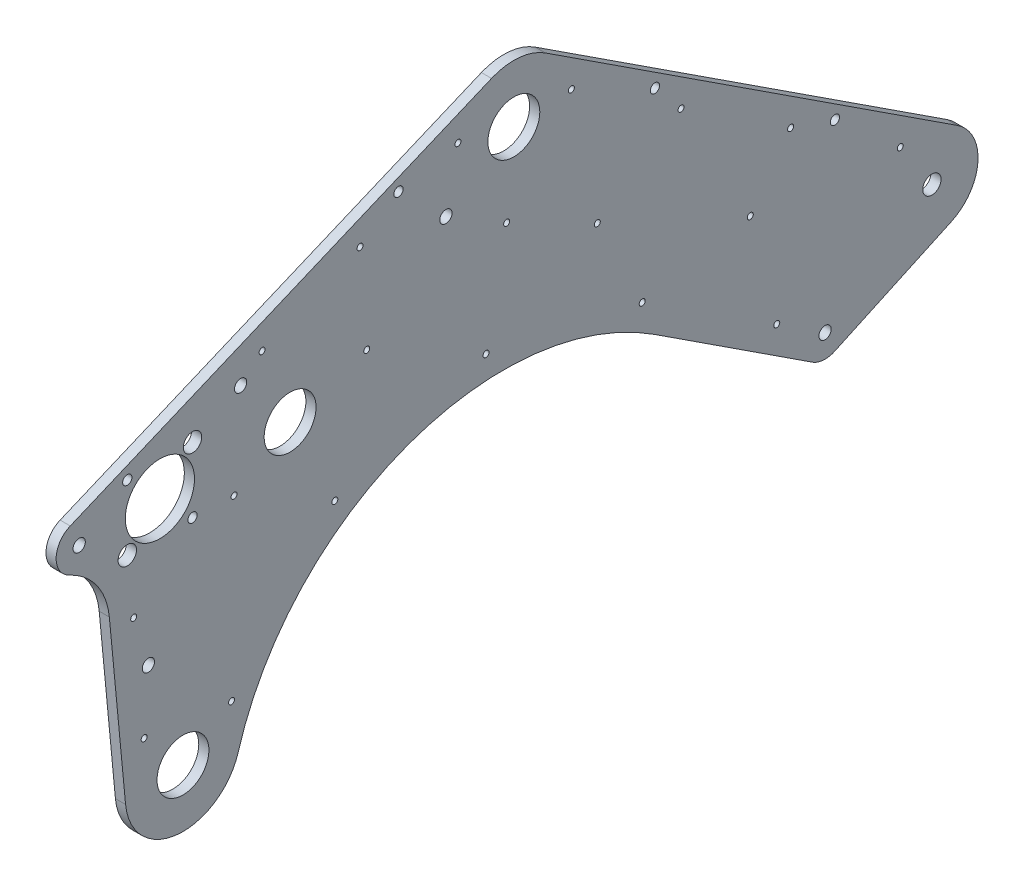
SolidWorks part; units mm, degrees
material "Acrylic (Medium-high impact)"
ref_plane "Front" through (0, 0, 0) normal (0, 0, 1) x (1, 0, 0)
ref_plane "Top" through (0, 0, 0) normal (0, 1, 0) x (1, 0, 0)
ref_plane "Right" through (0, 0, 0) normal (1, 0, 0) x (0, 0, -1)
sketch "Sketch1" plane through (0, 0, 0) normal (1, 0, 0) x (0, 0, -1)
  line L0 (-109.5375, -69.85) -> (-109.5375, -196.85)
  line L1 (-109.5375, -196.85) -> (-160.3375, -196.85)
  line L2 (-192.0875, -165.1) -> (-192.0875, -101.6)
  line L3 (-160.3375, -69.85) -> (-109.5375, -69.85)
  line L4 (-28.6872, -260.35) -> (-968.3377, -260.35) construction
  line L5 (-414.3375, -165.1) -> (-414.3375, -101.6) construction
  line L6 (-101.6, -57.15) -> (-76.2, -57.15)
  line L7 (-101.6, -57.15) -> (-101.6, -82.55)
  line L8 (-101.6, -82.55) -> (-76.2, -82.55)
  line L9 (-76.2, -57.15) -> (-76.2, -82.55)
  line L10 (-160.3375, 152.4) -> (-109.5375, 152.4) construction
  line L11 (-412.4442, -70.6452) -> (-160.3375, -101.6) construction
  line L12 (-353.4405, 63.4068) -> (-160.3375, -101.6) construction
  line L13 (-230.2306, 142.5945) -> (-160.3375, -101.6) construction
  line L14 (-435.3258, -60.5737) -> (-376.322, 73.4782)
  line L15 (-330.5589, 53.3353) -> (-389.5627, -80.7166)
  line L16 (-366.9572, 84.4377) -> (-243.7472, 163.6254)
  line L17 (-109.5375, -69.85) -> (-109.5375, 357.098) construction
  line L18 (-216.7139, 121.5636) -> (-339.9238, 42.3759)
  line L19 (-515.9375, 289.2974) -> (-515.9375, -104.2984) construction
  line L22 (-400.2568, 65.0845) -> (-387.5568, -68.2751)
  line L23 (-437.3316, -73.0152) -> (-450.0316, 60.3444)
  circle A0 centre (0, 0) radius 5.0419
  circle A1 centre (-412.4442, -70.6452) radius 11.557
  circle A2 centre (-353.4405, 63.4068) radius 11.557
  circle A3 centre (-230.2306, 142.5945) radius 11.557
  arc A4 (-160.3375, -196.85) -> (-192.0875, -165.1) centre (-160.3375, -165.1) cw
  arc A5 (-192.0875, -101.6) -> (-160.3375, -69.85) centre (-160.3375, -101.6) cw
  circle A6 centre (-309.0551, -144.1658) radius 120.65
  arc A7 (-414.3375, -101.6) -> (-160.3375, 152.4) centre (-160.3375, -101.6) cw construction
  circle A12 centre (-425.1442, 62.7144) radius 31.75
  arc A15 (-389.5627, -80.7166) -> (-435.3258, -60.5737) centre (-412.4442, -70.6452) cw
  arc A16 (-376.322, 73.4782) -> (-330.5589, 53.3353) centre (-353.4405, 63.4068) cw
  arc A17 (-339.9238, 42.3759) -> (-366.9572, 84.4377) centre (-353.4405, 63.4068) cw
  arc A18 (-243.7472, 163.6254) -> (-216.7139, 121.5636) centre (-230.2306, 142.5945) cw
  arc A21 (-450.0316, 60.3444) -> (-400.2568, 65.0845) centre (-425.1442, 62.7144) cw
  arc A22 (-387.5568, -68.2751) -> (-437.3316, -73.0152) centre (-412.4442, -70.6452) cw
  circle B0 centre (-230.2306, 142.5945) radius 25
  circle B1 centre (-353.4405, 63.4068) radius 25
  circle B2 centre (-412.4442, -70.6452) radius 25
  circle B3 centre (-425.1442, 62.7144) radius 25
  dimension "D1" = 10.0838
  dimension "D2" = 23.114
  dimension "D4" = 31.75
  dimension "D10" = 241.3
  dimension "D19" = 63.5
  dimension "D26" = 70.6452
  dimension "D27" = 412.4442
  dimension "D3" = 127
  dimension "D5" = 82.55
  dimension "D6" = 190.5
  dimension "D7" = 25.4
  dimension "D8" = 7.9375
  dimension "D9" = 203.2
  dimension "D12" = 101.6
  dimension "D13" = 57.15
  dimension "D14" = 33.514
  dimension "D15" = 33.514
  dimension "D16" = 7
  dimension "D24" = 406.4
  dimension "D21" = 12.7
  dimension "D11" = 222.25
sketch_block_instance "Block1-1"
sketch_block "Block1" parameters "D1"=50
sketch_block_instance "Block2-1"
sketch_block "Block2" parameters "D1"=40
sketch_block_instance "Block3-1"
sketch_block "Block3" parameters "D1"=40
sketch_block_instance "Block4-1"
sketch_block "Block4" parameters "D1"=50
other "Belt1"
other "Belt2"
other "Belt4"
sketch "Sketch3" plane through (0, 0, 0) normal (1, 0, 0) x (0, 0, -1)
  line L0 (-412.4442, -70.6452) -> (0, 0) construction
  line L1 (0, 0) -> (-58.8496, -41.2069) construction
  line L2 (0, 0) -> (-70.6452, 412.4442) construction
  line L3 (0, 0) -> (-41.2069, 58.8496) construction
  line L4 (-58.8496, -41.2069) -> (-64.0291, -10.9672) construction
  line L5 (-41.2069, 58.8496) -> (-10.9672, 64.0291) construction
  line L6 (-41.2069, 58.8496) -> (-58.8496, -41.2069)
  line L7 (-0.9596, 287.1034) -> (-41.2069, 58.8496)
  line L8 (0, 0) -> (142.5945, 230.2306) construction
  line L9 (0, 0) -> (-230.2306, 142.5945) construction
  line L10 (-230.2306, 142.5945) -> (-199.9405, -34.2466) construction
  line L11 (142.5945, 230.2306) -> (-34.2466, 199.9405) construction
  circle A0 centre (-70.6452, 412.4442) radius 25.4
  dimension "D1" = 50.8
  dimension "D2" = 90
  dimension "D3" = 101.6
  dimension "D4" = 231.775
  dimension "D5" = 80
sketch "Sketch2" plane through (0, 0, 0) normal (1, 0, 0) x (0, 0, -1)
  line L0 (-444.0512, -73.6552) -> (-452.991, 20.2192)
  line L1 (-474.5125, 74.4234) -> (-242.5262, 171.867)
  line L2 (-412.4442, -70.6452) -> (-412.4442, 0) construction
  line L4 (13.8769, 21.2742) -> (-212.8845, 169.1873)
  line L7 (-65.788, -51.844) -> (-152.593, 4.7776)
  line L10 (-53.5189, -52.734) -> (10.6613, -23.0542)
  line L13 (-443.1047, 44.7539) -> (-407.1837, 80.675) construction
  line L14 (-443.1047, 80.675) -> (-407.1837, 44.7539) construction
  line L15 (-353.4405, 63.4068) -> (-230.2306, 142.5945) construction
  circle A0 centre (-230.2306, 142.5945) radius 14.2875
  circle A1 centre (-353.4405, 63.4068) radius 14.2875
  circle A2 centre (-412.4442, -70.6452) radius 14.2875
  circle A3 centre (-425.1442, 62.7144) radius 19.05
  circle A9 centre (0, 0) radius 5.0419 construction
  circle A10 centre (0, 0) radius 5.0419
  arc A13 (-444.0512, -73.6552) -> (-381.9977, -79.6491) centre (-412.4442, -70.6452) ccw
  arc A16 (10.6613, -23.0542) -> (13.8769, 21.2742) centre (0, 0) ccw
  arc A18 (-152.593, 4.7776) -> (-381.9977, -79.6491) centre (-235.8542, -122.8677) ccw
  circle A19 centre (-58.8496, -41.2069) radius 3.3782
  circle A22 centre (-267.6235, 118.5618) radius 3.3782
  circle A24 centre (-230.2306, 142.5945) radius 31.75 construction
  circle A27 centre (-407.1837, 80.675) radius 5.08
  circle A28 centre (-443.1047, 80.675) radius 2.5527
  circle A29 centre (-443.1047, 44.7539) radius 5.08
  circle A30 centre (-407.1837, 44.7539) radius 2.5527
  circle A31 centre (-425.1442, 62.7144) radius 25.4 construction
  circle A32 centre (-469.5942, 62.7144) radius 3.3782
  arc A34 (-474.5125, 74.4234) -> (-474.9255, 51.1876) centre (-469.5942, 62.7144) ccw
  arc A35 (-474.9255, 51.1876) -> (-452.991, 20.2192) centre (-490.9194, 16.6072) cw
  circle A37 centre (-425.1442, 62.7144) radius 31.75 construction
  circle A38 centre (-469.5942, 62.7144) radius 7.9375 construction
  circle A39 centre (-431.4942, -13.4856) radius 3.3782
  circle A40 centre (-431.4942, -13.4856) radius 7.9375 construction
  circle A41 centre (-380.6942, 94.4644) radius 3.3782
  arc A42 (-65.788, -51.844) -> (-53.5189, -52.734) centre (-58.8496, -41.2069) ccw
  arc A43 (-242.5262, 171.867) -> (-212.8845, 169.1873) centre (-230.2306, 142.5945) cw
  circle A44 centre (-353.4405, 63.4068) radius 11.557 construction
  point P5 (0, 0)
  dimension "D1" = 28.575
  dimension "D2" = 38.1
  dimension "D3" = 44.45
  dimension "D4" = 63.5
  dimension "D5" = 12.7
  dimension "D7" = 25.4
  dimension "D8" = 152.4
  dimension "D10" = 6.7564
  dimension "D11" = 6.7564
  dimension "D12" = 15.875
  dimension "D17" = 15.875
  dimension "D18" = 5.1054
  dimension "D19" = 10.16
  dimension "D20" = 50.8
  dimension "D21" = 31.75
  dimension "D22" = 38.1
  dimension "D23" = 6.35
  dimension "D16" = 44.45
  dimension "D15" = 31.75
  dimension "D24" = 76.2
  dimension "D25" = 44.45
  dimension "D9" = 12.7
extrude "Boss-Extrude1" add sketch "Sketch2" along normal blind 5.588
sketch "Sketch4" plane through (5.588, 0, 0) normal (1, 0, 0) x (0, 0, -1)
  line L0 (-353.4405, 63.4068) -> (-230.2306, 142.5945) construction
  line L1 (-242.5262, 171.867) -> (-474.5125, 74.4234) construction
  line L2 (13.8769, 21.2742) -> (-212.8845, 169.1873) construction
  line L3 (-293.7616, 143.4587) -> (-434.2697, 84.4396) construction
  line L4 (-434.2697, 84.4396) -> (-425.1442, 62.7144) construction
  line L5 (-230.2306, 142.5945) -> (-216.3537, 163.8687) construction
  line L11 (-231.5885, 173.8062) -> (10.4076, 15.9557) construction
  line L14 (-231.5885, 173.8062) -> (-267.6235, 118.5618) construction
  line L15 (0, 0) -> (10.4076, 15.9557) construction
  circle A4 centre (-293.7616, 143.4587) radius 2.5527
  circle A5 centre (-152.531, 122.2382) radius 2.5527
  circle A6 centre (-53.415, 57.5863) radius 2.5527
  dimension "D1" = 6.35
  dimension "D2" = 5.1054
  dimension "D3" = 152.4
  dimension "D4" = 6.35
  dimension "D5" = 76.2
  dimension "D6" = 76.2
extrude "Cut-Extrude1" cut sketch "Sketch4" against normal through all
sketch "Sketch6" plane through (5.588, 0, 0) normal (1, 0, 0) x (0, 0, -1)
  line L0 (-17.4343, 26.5351) -> (-77.8057, 65.9145) construction
  line L1 (-368.8477, 105.0321) -> (-314.9368, 127.6768) construction
  line L2 (-314.9368, 127.6768) -> (-261.026, 150.3215) construction
  line L3 (-385.6942, -53.5425) -> (-328.8245, 13.5674) construction
  line L4 (-58.8496, -41.2069) -> (-145.6546, 15.4147)
  line L5 (-58.8496, -41.2069) -> (-145.6546, 15.4147) construction
  line L6 (-328.8245, 13.5674) -> (-245.5627, 41.9466) construction
  line L7 (-245.5627, 41.9466) -> (-159.5448, 23.5389) construction
  line L8 (-159.5448, 23.5389) -> (-85.4423, -23.8608) construction
  line L9 (-77.8057, 65.9145) -> (-138.1772, 105.2939) construction
  line L10 (-242.5262, 171.867) -> (-474.5125, 74.4234) construction
  line L11 (13.8769, 21.2742) -> (-212.8845, 169.1873) construction
  line L12 (-138.1772, 105.2939) -> (-198.5487, 144.6733) construction
  line L13 (-439.5653, 13.2018) -> (-433.8164, -47.1656) construction
  line L14 (-452.991, 20.2192) -> (-444.0512, -73.6552) construction
  line L15 (-234.1843, 98.8607) -> (-311.2435, 76.7833) construction
  line L16 (-311.2435, 76.7833) -> (-384.2952, 43.7835) construction
  line L17 (-261.026, 150.3215) -> (-234.1843, 98.8607) construction
  line L18 (-234.1843, 98.8607) -> (-198.5487, 144.6733) construction
  line L19 (-234.1843, 98.8607) -> (-245.5627, 41.9466) construction
  line L20 (-439.5653, 13.2018) -> (-384.2952, 43.7835) construction
  line L21 (-384.2952, 43.7835) -> (-368.8477, 105.0321) construction
  line L22 (-384.2952, 43.7835) -> (-328.8245, 13.5674) construction
  line L23 (-329.9687, 121.3628) -> (-292.5183, 32.2038) construction
  line L24 (-159.5448, 23.5389) -> (-184.2774, 73.6729) construction
  line L25 (-184.2774, 73.6729) -> (-138.1772, 105.2939) construction
  line L26 (-234.1843, 98.8607) -> (-184.2774, 73.6729) construction
  line L27 (-77.8057, 65.9145) -> (-100.0255, 34.9646) construction
  line L28 (-100.0255, 34.9646) -> (-85.4423, -23.8608) construction
  line L29 (-100.0255, 34.9646) -> (-159.5448, 23.5389) construction
  line L30 (-242.5262, 171.867) -> (-474.5125, 74.4234) construction
  circle A0 centre (-17.4343, 26.5351) radius 1.651
  circle A1 centre (-159.5448, 23.5389) radius 1.651
  circle A2 centre (-77.8057, 65.9145) radius 1.651
  circle A3 centre (-245.5627, 41.9466) radius 1.651
  circle A4 centre (-261.026, 150.3215) radius 1.651
  circle A5 centre (-328.8245, 13.5674) radius 1.651
  circle A6 centre (-385.6942, -53.5425) radius 1.651
  circle A7 centre (-439.5653, 13.2018) radius 1.651
  circle A8 centre (-314.9368, 127.6768) radius 1.651
  circle A9 centre (-368.8477, 105.0321) radius 1.651
  circle A10 centre (-138.1772, 105.2939) radius 1.651
  circle A11 centre (-85.4423, -23.8608) radius 1.651
  circle A13 centre (-380.6942, 94.4644) radius 3.3782 construction
  arc A14 (-145.6546, 15.4147) -> (-394.1763, -76.0475) centre (-235.8542, -122.8677) ccw
  arc A15 (-145.6546, 15.4147) -> (-394.1763, -76.0475) centre (-235.8542, -122.8677) ccw construction
  circle A17 centre (-433.8164, -47.1656) radius 1.651
  circle A18 centre (-198.5487, 144.6733) radius 1.651
  circle A19 centre (-443.1047, 44.7539) radius 5.08 construction
  circle A20 centre (0, 0) radius 5.0419 construction
  circle A22 centre (-234.1843, 98.8607) radius 1.651
  circle A23 centre (-384.2952, 43.7835) radius 1.651
  circle A24 centre (-311.2435, 76.7833) radius 1.651
  circle A25 centre (-184.2774, 73.6729) radius 1.651
  circle A26 centre (-100.0255, 34.9646) radius 1.651
  point P20 (-433.8521, -46.7907)
  point P23 (-368.6103, 105.1318)
  point P48 (-194.8138, 142.2371)
  point P49 (-269.5117, 145.2675)
  point P64 (0, 0)
  point P65 (0, 0)
  dimension "D1" = 3.302
  dimension "D2" = 12.7
  dimension "D5" = 12.7
  dimension "D7" = 31.75
  dimension "D6" = 15.875
  dimension "D3" = 31.75
  dimension "D4" = 31.75
  dimension "D8" = 12.7
  dimension "D9" = 31.75
  dimension "D10" = 31.75
  dimension "D11" = 12.7
  dimension "D12" = 31.75
  dimension "D13" = 31.75
  dimension "D14" = 38.1
extrude "Cut-Extrude2" cut sketch "Sketch6" against normal through all
